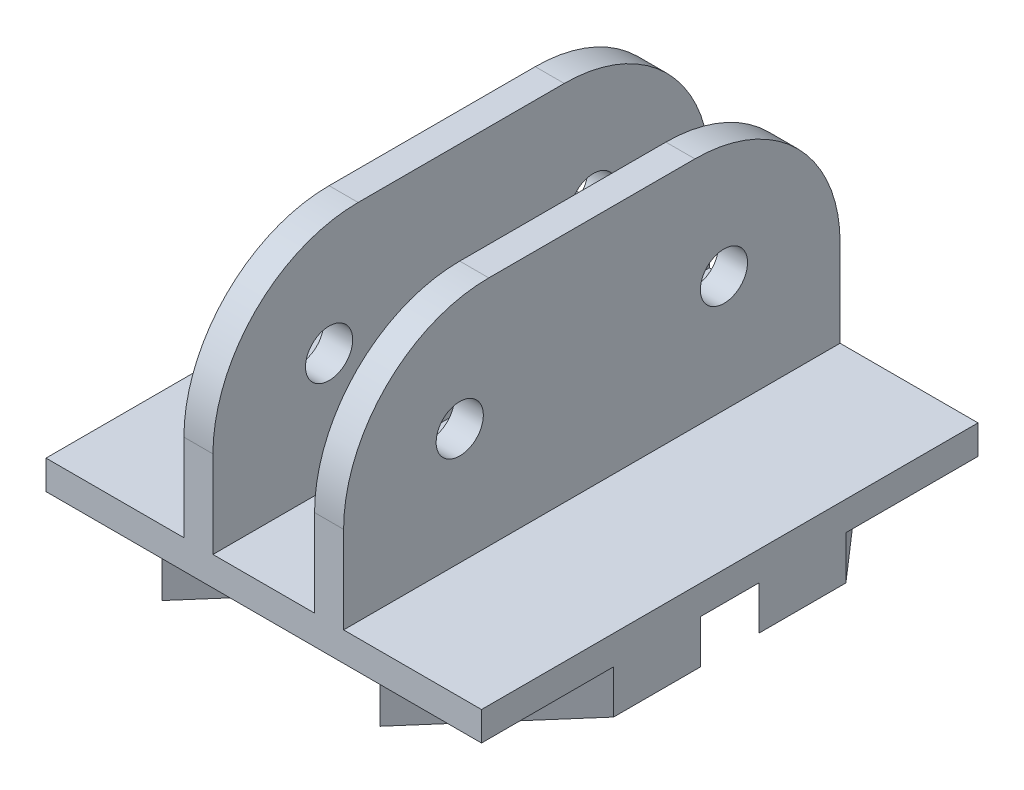
SolidWorks part; units mm, degrees
ref_plane "Front Plane" through (0, 0, 0) normal (0, 0, 1) x (1, 0, 0)
ref_plane "Top Plane" through (0, 0, 0) normal (0, 1, 0) x (1, 0, 0)
ref_plane "Right Plane" through (0, 0, 0) normal (1, 0, 0) x (0, 0, -1)
sketch "Sketch1" plane through (0, 0, 0) normal (0, 0, 1) x (1, 0, 0)
  line L0 (-5.5, 17) -> (-3.5, 17)
  line L1 (-3.5, 17) -> (-3.5, 1)
  line L2 (-3.5, 1) -> (3.5, 1)
  line L3 (15, -1) -> (-15, -1)
  line L5 (-8.8784, 9) -> (0, 9) construction
  line L6 (0, 1) -> (0, -1) construction
  line L7 (5.5, 17) -> (3.5, 17)
  line L9 (3.5, 17) -> (3.5, 1)
  line L10 (-5.5, 17) -> (-5.5, 1)
  line L11 (-5.5, 1) -> (-15, 1)
  line L12 (-15, 1) -> (-15, -1)
  line L13 (0, -9.9) -> (0, 9.9) construction
  line L14 (15, 1) -> (15, -1)
  line L15 (5.5, 1) -> (15, 1)
  line L16 (5.5, 17) -> (5.5, 1)
  point P8 (0, 0)
  dimension "D1" = 8
  dimension "D2" = 2
  dimension "D3" = 2
  dimension "D4" = 7
  dimension "D5" = 8
  dimension "D6" = 30
extrude "Boss-Extrude1" add sketch "Sketch1" along normal mid plane 34.2
fillet "Fillet1" radius 10 4 edges at (4.5, 17, -17.1) (-4.5, 17, -17.1) (-4.5, 17, 17.1) (4.5, 17, 17.1)
sketch "Sketch5" plane through (-5.5, 0, 0) normal (-1, 0, 0) x (0, 0, 1)
  line L0 (0, -9.9) -> (0, 9.9) construction
  line L1 (7.1, 17) -> (-7.1, 17) construction
  line L2 (-17.1, 7) -> (-17.1, 1) construction
  circle A0 centre (-9.1, 9) radius 1.625
  circle A1 centre (9.1, 9) radius 1.625
  dimension "D3" = 3.25
  dimension "D1" = 8
  dimension "D2" = 8
extrude "Cut-Extrude1" cut sketch "Sketch5" against normal through all
sketch "Sketch7" plane through (0, -1, 0) normal (0, -1, 0) x (1, 0, 0)
  line L0 (-15, 8) -> (-7.5, 16.6)
  line L1 (-15, 17.1) -> (-15, -17.1) construction
  line L2 (-7.5, 16.6) -> (0, 8)
  line L3 (-15, 8) -> (0, 8) construction
  line L4 (-15, 8) -> (-15, 2)
  line L5 (-15, 2) -> (-7.5, 10.6)
  line L6 (-7.5, 10.6) -> (0, 2)
  line L7 (0, -9.9) -> (0, 9.9) construction
  line L8 (15, 8) -> (15, 2)
  line L9 (15, 8) -> (7.5, 16.6)
  line L10 (15, 2) -> (7.5, 10.6)
  line L11 (7.5, 10.6) -> (0, 2)
  line L12 (7.5, 16.6) -> (0, 8)
  line L13 (-15, 17.1) -> (15, 17.1) construction
  line L14 (9.9, 0) -> (-9.9, 0) construction
  line L15 (-15, -2) -> (-7.5, -10.6)
  line L16 (-15, -8) -> (-15, -2)
  line L17 (-15, -8) -> (-7.5, -16.6)
  line L18 (-7.5, -16.6) -> (0, -8)
  line L19 (7.5, -16.6) -> (0, -8)
  line L20 (15, -8) -> (7.5, -16.6)
  line L21 (15, -8) -> (15, -2)
  line L22 (15, -2) -> (7.5, -10.6)
  line L23 (7.5, -10.6) -> (0, -2)
  line L24 (-7.5, -10.6) -> (0, -2)
  point P6 (-7.5, 8)
  dimension "D1" = 6
  dimension "D2" = 0.5
  dimension "D3" = 2
extrude "Boss-Extrude2" add sketch "Sketch7" along normal blind 3
